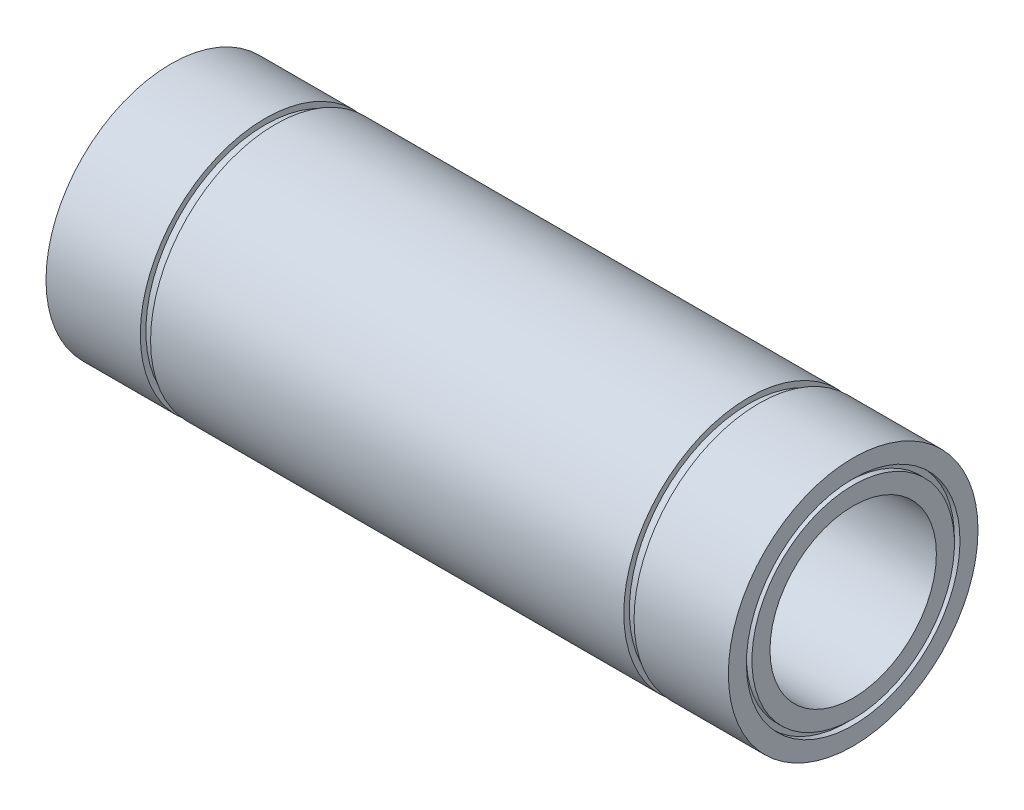
SolidWorks part; units mm, degrees
material "Ст3сп ГОСТ 535-2005"
ref_plane "Plano frontal" through (0, 0, 0) normal (0, 0, 1) x (1, 0, 0)
ref_plane "Plano superior" through (0, 0, 0) normal (0, 1, 0) x (1, 0, 0)
ref_plane "Plano direito" through (0, 0, 0) normal (1, 0, 0) x (0, 0, -1)
sketch "Esboço1" plane through (0, 0, 0) normal (0, 0, 1) x (1, 0, 0)
  line L0 (-61.5, 22.5) -> (-44.5, 22.5)
  line L1 (-44.5, 22.5) -> (-44.5, 21.5)
  line L2 (-44.5, 21.5) -> (-42.65, 21.5)
  line L3 (-42.65, 21.5) -> (-42.65, 22.5)
  line L4 (-42.65, 22.5) -> (42.65, 22.5)
  line L5 (42.65, 22.5) -> (42.65, 21.5)
  line L6 (42.65, 21.5) -> (44.5, 21.5)
  line L7 (44.5, 21.5) -> (44.5, 22.5)
  line L8 (44.5, 22.5) -> (61.5, 22.5)
  line L9 (61.5, 22.5) -> (61.5, 19.25)
  line L10 (61.5, 15) -> (-61.5, 15)
  line L11 (-61.5, 15) -> (-61.5, 18.25)
  line L12 (0, 15) -> (0, 0) construction
  line L13 (0, 0) -> (-86.5, 0) construction
  line L14 (-61.5, 19.25) -> (-61.5, 22.5)
  line L15 (-61.5, 19.25) -> (-60.5, 19.25)
  line L16 (61.5, 18.25) -> (61.5, 15)
  line L17 (-60.5, 19.25) -> (-60.5, 18.25)
  line L18 (-60.5, 18.25) -> (-61.5, 18.25)
  line L19 (61.5, 19.25) -> (60.5, 19.25)
  line L21 (61.5, 18.25) -> (60.5, 18.25)
  line L22 (60.5, 19.25) -> (60.5, 18.25)
  dimension "D1" = 123
  dimension "D2" = 89
  dimension "D3" = 1.85
  dimension "D4" = 30
  dimension "D5" = 45
  dimension "D6" = 43
  dimension "D7" = 1
  dimension "D8" = 1
  dimension "D9" = 1
  dimension "D10" = 1
revolve "Revolução1" add sketch "Esboço1" angle 360 about L13
